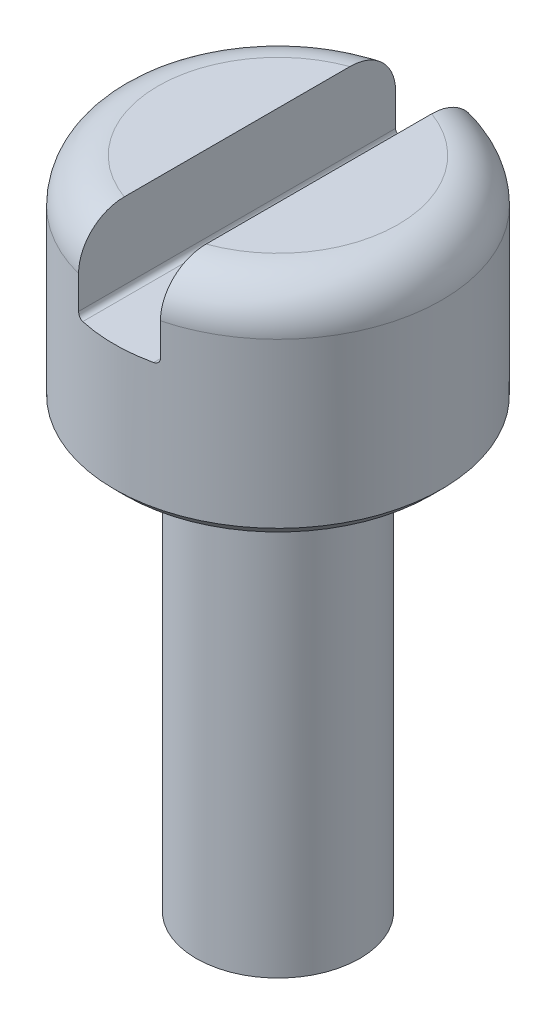
SolidWorks part; units mm, degrees
ref_plane "Front Plane" through (0, 0, 0) normal (0, 0, 1) x (1, 0, 0)
ref_plane "Top Plane" through (0, 0, 0) normal (0, 1, 0) x (1, 0, 0)
ref_plane "Right Plane" through (0, 0, 0) normal (1, 0, 0) x (0, 0, -1)
sketch "Sketch1" plane through (0, 0, 0) normal (0, 1, 0) x (1, 0, 0)
  circle A0 centre (0, 0) radius 1.5
  dimension "D1" = 3
extrude "Boss-Extrude1" add sketch "Sketch1" along normal blind 2
sketch "Sketch2" plane through (0, 0, 0) normal (0, 0, 1) x (1, 0, 0)
  line L0 (0, -0.4861) -> (0, 2.5543) construction
  line L1 (1.5, 2) -> (-1.5, 2) construction
  line L2 (-0.375, 2.75) -> (0.375, 2.75)
  line L3 (-0.375, 2.75) -> (-0.375, 1.25)
  line L4 (-0.375, 1.25) -> (0.375, 1.25)
  line L5 (0.375, 2.75) -> (0.375, 1.25)
  line L6 (-0.375, 2.75) -> (0.375, 1.25) construction
  line L7 (-0.375, 1.25) -> (0.375, 2.75) construction
  point P3 (0, 2)
  dimension "D1" = 0.75
  dimension "D2" = 0.75
extrude "Cut-Extrude1" cut sketch "Sketch2" against normal mid plane 12
sketch "Sketch3" plane through (0, 0, 0) normal (0, -1, 0) x (1, 0, 0)
  circle A0 centre (0, 0) radius 0.75
  dimension "D1" = 1.5
extrude "Boss-Extrude2" add sketch "Sketch3" along normal blind 4
fillet "Fillet1" radius 0.05 2 edges at (-0.375, 1.25, 0) (0.375, 1.25, 0)
chamfer "Chamfer2" distance 0.1 angle 45 1 edges at (0, 0, 1.5)
fillet "Fillet2" radius 0.4 2 edges at (1.5, 2, 0) (-1.5, 2, 0)
